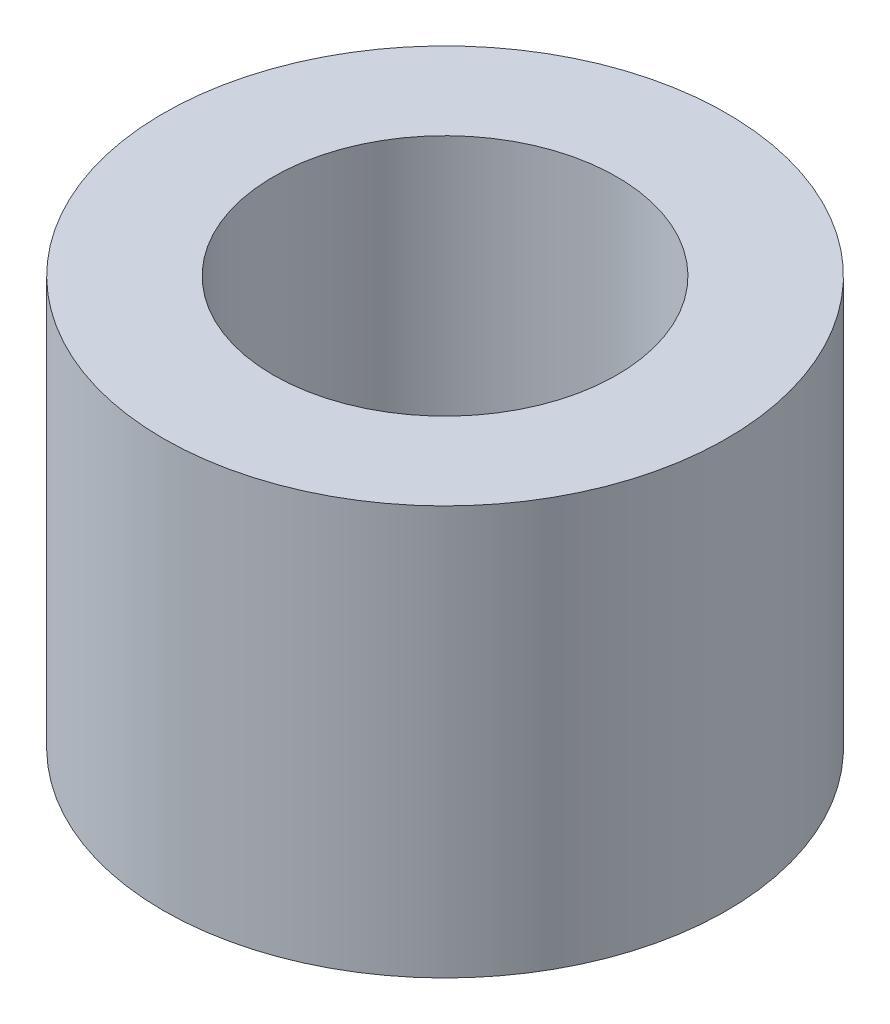
SolidWorks part; units mm, degrees
ref_plane "Front Plane" through (0, 0, 0) normal (0, 0, 1) x (1, 0, 0)
ref_plane "Top Plane" through (0, 0, 0) normal (0, 1, 0) x (1, 0, 0)
ref_plane "Right Plane" through (0, 0, 0) normal (1, 0, 0) x (0, 0, -1)
sketch "Sketch1" plane through (0, 0, 0) normal (0, 1, 0) x (1, 0, 0)
  circle A3 centre (59.4755, 35.57) radius 4.1
extrude "Boss-Extrude1" add sketch "Sketch1" along normal blind 5.95
hole_wizard "Tap Drill for M6 Tap1" positions "Sketch2" profile "Sketch3" hole size "M6" standard "ISO" end condition through all
sketch "Sketch2" plane through (0, 5.95, 0) normal (0, 1, 0) x (1, 0, 0)
  point P0 (59.4755, 35.57)
sketch "Sketch3" plane through (59.4755, 5.95, -35.57) normal (1, 0, 0) x (0, 0, 1)
  line L0 (0, 0) -> (0, 5.95)
  line L1 (0, 5.95) -> (2.5, 5.95)
  line L2 (2.5, 5.95) -> (2.5, 0)
  line L5 (2.5, 0) -> (0, 0)
  line L11 (0, -6.35) -> (0, 107.95) construction
  dimension "Thru Hole Dia." = 5
  dimension "Thru Hole Depth" = 5.95
